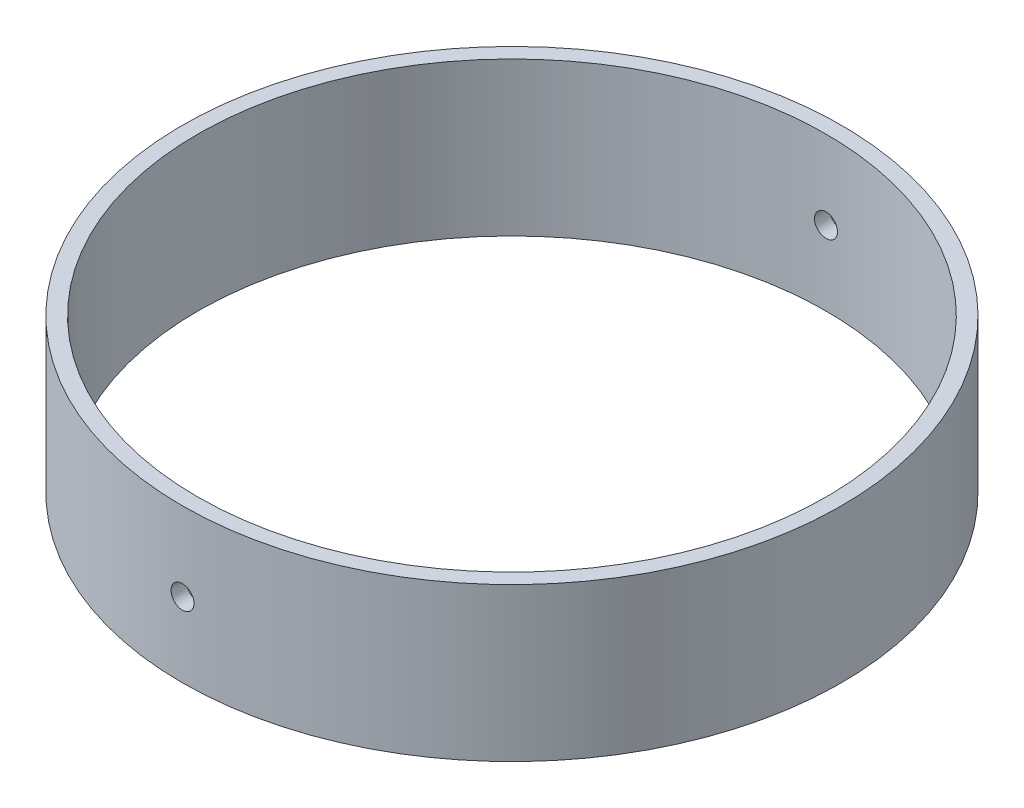
SolidWorks part; units mm, degrees
ref_plane "Front Plane" through (0, 0, 0) normal (0, 0, 1) x (1, 0, 0)
ref_plane "Top Plane" through (0, 0, 0) normal (0, 1, 0) x (1, 0, 0)
ref_plane "Right Plane" through (0, 0, 0) normal (1, 0, 0) x (0, 0, -1)
sketch "Sketch1" plane through (0, 0, 0) normal (0, 1, 0) x (1, 0, 0)
  circle A0 centre (0, 0) radius 52.07
  circle A1 centre (0, 0) radius 54.61
  dimension "D1" = 104.14
  dimension "D2" = 2.54
extrude "Boss-Extrude1" add sketch "Sketch1" along normal blind 25.4
sketch "Sketch3" plane through (0, 0, 0) normal (0, 0, 1) x (1, 0, 0)
  circle A0 centre (0, 12.329) radius 1.905
  dimension "D1" = 3.81
extrude "Cut-Extrude1" cut sketch "Sketch3" along normal through all
pattern_circular "CirPattern1" count 2 over 360 about axis through (0, 12.329, 0) along (0, 0, 1) of "Cut-Extrude1"
